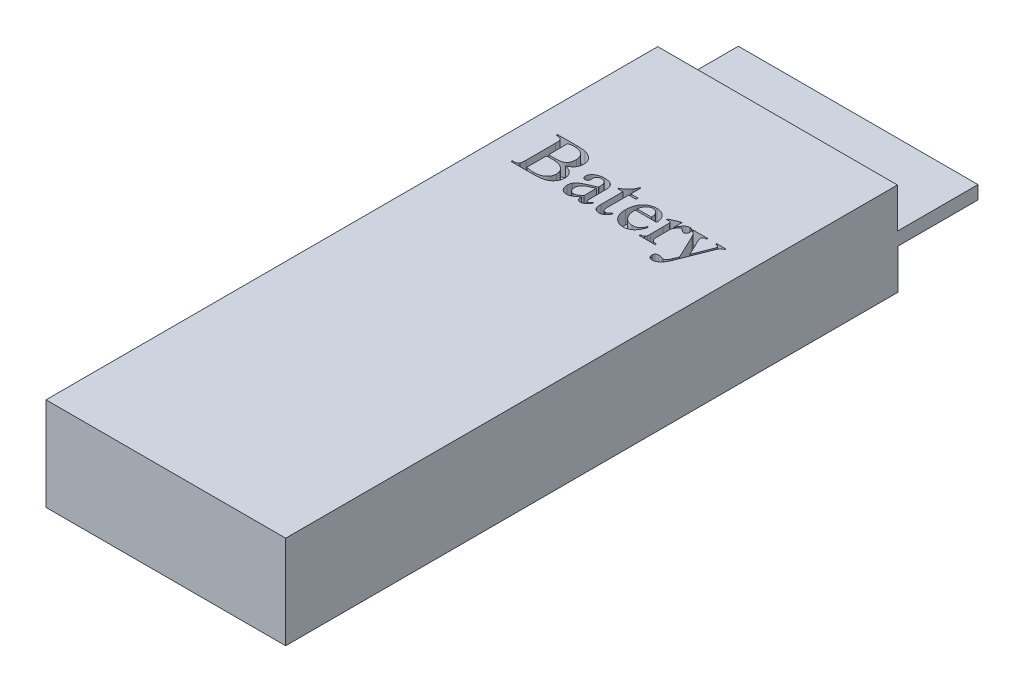
SolidWorks part; units mm, degrees
ref_plane "Alzado" through (0, 0, 0) normal (0, 0, 1) x (1, 0, 0)
ref_plane "Planta" through (0, 0, 0) normal (0, 1, 0) x (1, 0, 0)
ref_plane "Vista lateral" through (0, 0, 0) normal (1, 0, 0) x (0, 0, -1)
sketch "Croquis1" plane through (0, 0, 0) normal (0, 1, 0) x (1, 0, 0)
  line L1 (-9, 26) -> (9, 26)
  line L2 (-9, 26) -> (-9, -26)
  line L3 (-9, -26) -> (9, -26)
  line L4 (9, 26) -> (9, -26)
  line L5 (-9, 26) -> (9, -26) construction
  line L6 (-9, -26) -> (9, 26) construction
  point P0 (0, 0)
  dimension "D1" = 18
  dimension "D2" = 52
extrude "Saliente-Extruir1" add sketch "Croquis1" along normal blind 7
sketch "Croquis2" plane through (0, 7, 0) normal (0, 1, 0) x (1, 0, 0)
  line L0 (9, -26) -> (9, 26) construction
  line L1 (-9, 26) -> (9, 26)
  line L2 (-9, 26) -> (-9, 19.9463)
  line L3 (-9, 19.9463) -> (9, 19.9463)
  line L4 (9, 26) -> (9, 19.9463)
extrude "Cortar-Extruir1" cut sketch "Croquis2" against normal blind 3
sketch "Croquis3" plane through (0, 0, 0) normal (0, -1, 0) x (1, 0, 0)
  line L0 (-9, -26) -> (-9, 26) construction
  line L1 (-9, -19.9831) -> (9, -19.9831)
  line L2 (-9, -19.9831) -> (-9, -26)
  line L3 (-9, -26) -> (9, -26)
  line L4 (9, -19.9831) -> (9, -26)
extrude "Cortar-Extruir2" cut sketch "Croquis3" against normal blind 3
sketch "Croquis4" plane through (0, 7, 0) normal (0, 1, 0) x (1, 0, 0)
  text T0 "Batery\r\n\r\n" font "Times New Roman" height 3.5
extrude "Cortar-Extruir3" cut sketch "Croquis4" against normal blind 1
